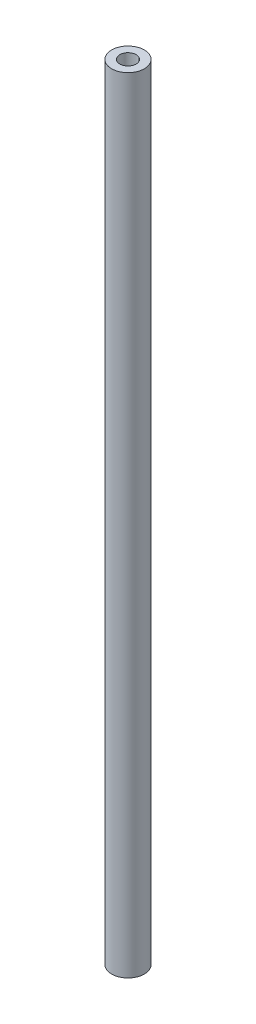
SolidWorks part; units mm, degrees
ref_plane "Front Plane" through (0, 0, 0) normal (0, 0, 1) x (1, 0, 0)
ref_plane "Top Plane" through (0, 0, 0) normal (0, 1, 0) x (1, 0, 0)
ref_plane "Right Plane" through (0, 0, 0) normal (1, 0, 0) x (0, 0, -1)
sketch "Sketch1" plane through (0, 0, 0) normal (0, 1, 0) x (1, 0, 0)
  circle A0 centre (0, 0) radius 5
  dimension "D1" = 10
extrude "Boss-Extrude1" add sketch "Sketch1" along normal blind 240
sketch "Sketch2" plane through (0, 240, 0) normal (0, 1, 0) x (1, 0, 0)
  circle A0 centre (0, 0) radius 2.5
  dimension "D1" = 5
extrude "Cut-Extrude1" cut sketch "Sketch2" against normal blind 30
